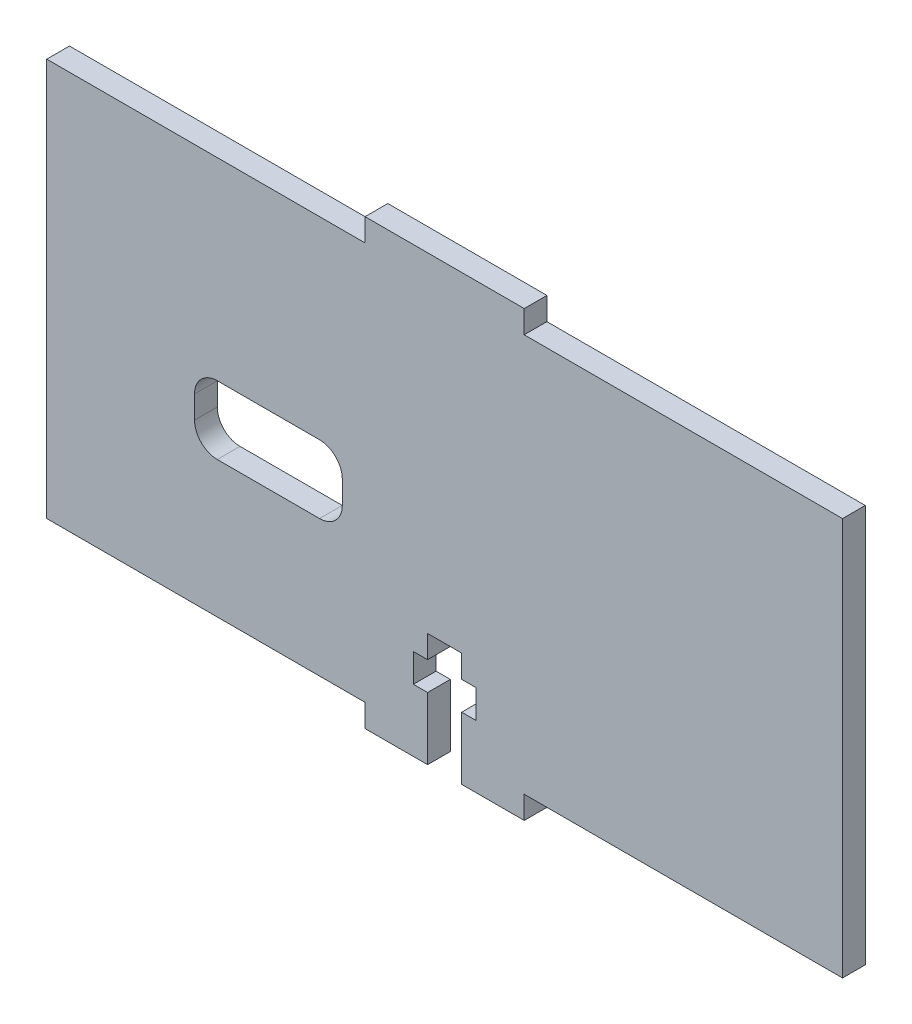
SolidWorks part; units mm, degrees
material "Acrylic (Medium-high impact)"
ref_plane "Front Plane" through (0, 0, 0) normal (0, 0, 1) x (1, 0, 0)
ref_plane "Top Plane" through (0, 0, 0) normal (0, 1, 0) x (1, 0, 0)
ref_plane "Right Plane" through (0, 0, 0) normal (1, 0, 0) x (0, 0, -1)
sketch "Sketch1" plane through (0, 0, 0) normal (0, 0, 1) x (1, 0, 0)
  line L0 (42, 35) -> (70, 35)
  line L1 (0, 0) -> (28, 0)
  line L2 (0, 0) -> (0, 35)
  line L3 (0, 35) -> (28, 35)
  line L4 (70, 0) -> (70, 35)
  line L5 (28, 37) -> (42, 37)
  line L6 (28, 0) -> (28, -2)
  line L7 (28, -2) -> (33.5, -2)
  line L8 (42, 0) -> (42, -2)
  line L9 (42, 0) -> (70, 0)
  line L10 (28, 35) -> (28, 37)
  line L11 (33.5, -2) -> (33.5, 3.5)
  line L12 (42, 35) -> (42, 37)
  line L13 (33.5, 3.5) -> (32.25, 3.5)
  line L14 (32.25, 3.5) -> (32.25, 6)
  line L15 (32.25, 6) -> (33.5, 6)
  line L16 (33.5, 6) -> (33.5, 8)
  line L17 (13, 18) -> (26, 18)
  line L18 (13, 18) -> (13, 12)
  line L19 (13, 12) -> (26, 12)
  line L20 (26, 18) -> (26, 12)
  line L21 (13, 18) -> (26, 12) construction
  line L22 (13, 12) -> (26, 18) construction
  line L23 (33.5, 8) -> (36.5, 8)
  line L24 (36.5, 8) -> (36.5, 6)
  line L25 (36.5, 6) -> (37.75, 6)
  line L26 (37.75, 6) -> (37.75, 3.5)
  line L27 (37.75, 3.5) -> (36.5, 3.5)
  line L28 (36.5, 3.5) -> (36.5, -2)
  line L29 (36.5, -2) -> (42, -2)
  line L30 (33.5, -2) -> (36.5, -2) construction
  line L31 (35, 8) -> (35, -2) construction
  point P16 (19.5, 15)
  dimension "D1" = 2
  dimension "D2" = 70
  dimension "D3" = 35
  dimension "D4" = 14
  dimension "D5" = 28
  dimension "D6" = 13
  dimension "D7" = 6
  dimension "D8" = 15
  dimension "D9" = 13
  dimension "D10" = 3
  dimension "D11" = 10
  dimension "D12" = 2
  dimension "D13" = 2.5
  dimension "D14" = 5.5
extrude "Main Slider Side Up" add sketch "Sketch1" along normal blind 2
fillet "Slider Side Up Contouring" radius 2 4 edges at (13, 12, 1) (26, 12, 1) (26, 18, 1) (13, 18, 1)
